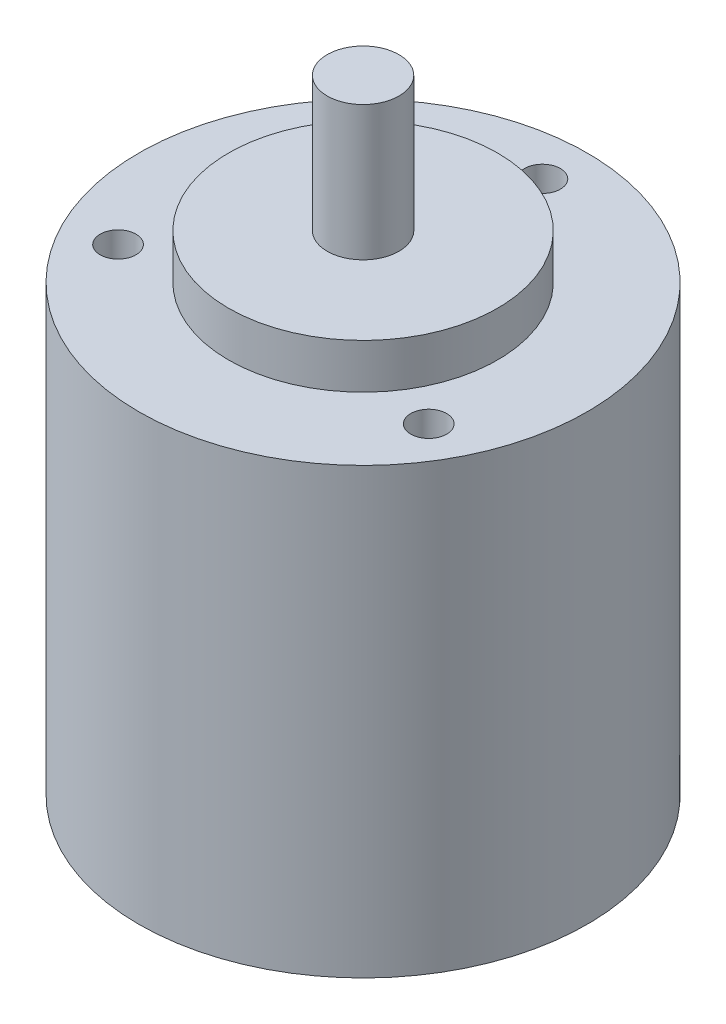
SolidWorks part; units mm, degrees
ref_plane "Front" through (0, 0, 0) normal (0, 0, 1) x (1, 0, 0)
ref_plane "Top" through (0, 0, 0) normal (0, 1, 0) x (1, 0, 0)
ref_plane "Right" through (0, 0, 0) normal (1, 0, 0) x (0, 0, -1)
sketch "Sketch1" plane through (0, 0, 0) normal (0, 1, 0) x (1, 0, 0)
  circle A0 centre (0, 0) radius 25
  dimension "D1" = 50
extrude "Boss-Extrude1" add sketch "Sketch1" along normal blind 49.5
sketch "Sketch2" plane through (0, 49.5, 0) normal (0, 1, 0) x (1, 0, 0)
  circle A0 centre (0, 0) radius 15
  dimension "D1" = 30
extrude "Boss-Extrude2" add sketch "Sketch2" along normal blind 5
sketch "Sketch3" plane through (0, 54.5, 0) normal (0, 1, 0) x (1, 0, 0)
  circle A0 centre (0, 0) radius 4
  dimension "D1" = 8
extrude "Boss-Extrude3" add sketch "Sketch3" along normal blind 15
sketch "Sketch4" plane through (0, 49.5, 0) normal (0, 1, 0) x (1, 0, 0)
  circle A0 centre (0, 0) radius 20 construction
  circle A1 centre (0, 20) radius 2
  circle A2 centre (17.3205, -10) radius 2
  circle A3 centre (-17.3205, -10) radius 2
  point P5 (-11.2149, -13.1897)
  point P6 (0, 0)
  point P11 (0, 0)
  dimension "D1" = 40
  dimension "D2" = 4
  dimension "D3" = 3
extrude "Cut-Extrude1" cut sketch "Sketch4" against normal blind 10
